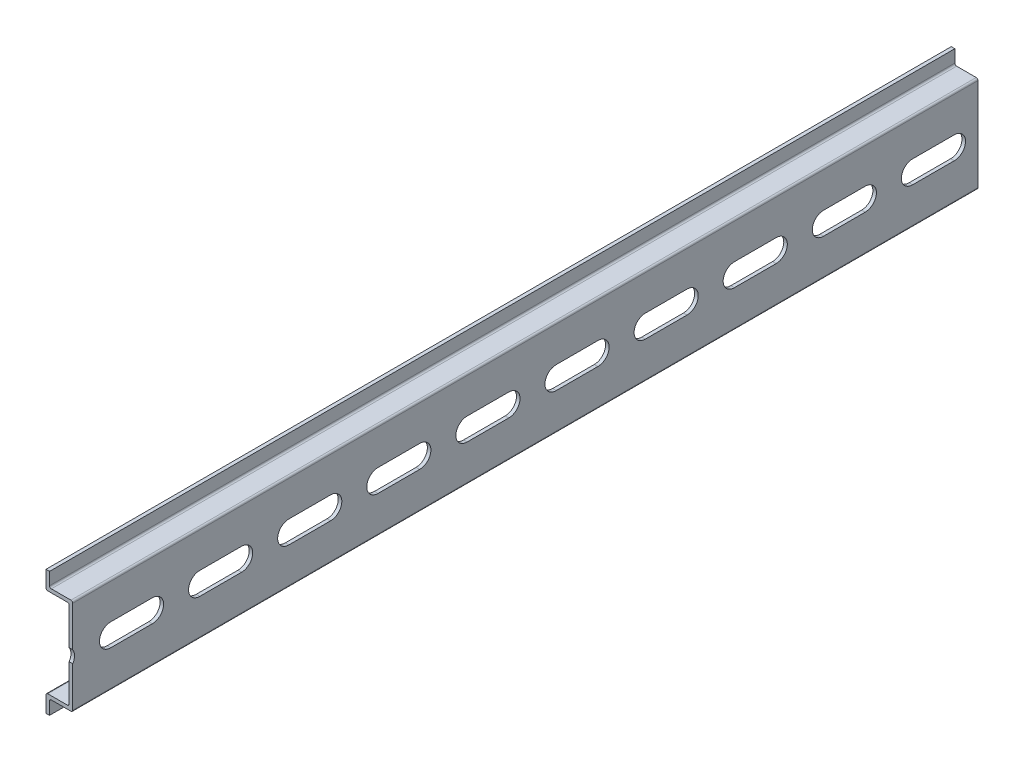
SolidWorks part; units mm, degrees
ref_plane "Front Plane" through (0, 0, 0) normal (0, 0, 1) x (1, 0, 0)
ref_plane "Top Plane" through (0, 0, 0) normal (0, 1, 0) x (1, 0, 0)
ref_plane "Right Plane" through (0, 0, 0) normal (1, 0, 0) x (0, 0, -1)
sketch "profile" plane through (0, 0, 0) normal (0, 0, 1) x (1, 0, 0)
  line L0 (0, -13.5) -> (0, 13.5) construction
  line L1 (0, 13.5) -> (-6.5, 13.5) construction
  line L2 (-6.5, 13.5) -> (-6.5, 17.5) construction
  line L3 (0, -13.5) -> (-6.5, -13.5) construction
  line L4 (-6.5, -13.5) -> (-6.5, -17.5) construction
  dimension "D1" = 27
  dimension "D2" = 35
  dimension "D3" = 6.5
sketch "Sketch3" plane through (0, 0, 0) normal (0, 0, 1) x (1, 0, 0)
  line L0 (-6.5, -13.5) -> (-6.5, -17.5) construction
  line L1 (0, -13.5) -> (-6.5, -13.5) construction
  line L2 (0, -13.5) -> (0, 13.5) construction
  line L3 (0, 13.5) -> (-6.5, 13.5) construction
  line L4 (-6.5, 13.5) -> (-6.5, 17.5) construction
  line L5 (-6.5, -13.5) -> (-6.5, -17.5)
  line L6 (0, -13.5) -> (-6.5, -13.5)
  line L7 (0, -13.5) -> (0, 13.5)
  line L8 (0, 13.5) -> (-6.5, 13.5)
  line L9 (-6.5, 13.5) -> (-6.5, 17.5)
extrude "Extrude-Thin1" add sketch "Sketch3" along normal blind 449.2625 thin
sketch "Sketch4" plane through (0, 0, 0) normal (1, 0, 0) x (0, 0, -1)
  line L0 (0, 0) -> (-62.1077, 0) construction
  line L1 (-6.65, 0) -> (-18.35, 0) construction
  line L2 (-6.65, -3.15) -> (-18.35, -3.15)
  line L3 (-6.65, 3.15) -> (-18.35, 3.15)
  arc A0 (-6.65, -3.15) -> (-6.65, 3.15) centre (-6.65, 0) ccw
  arc A1 (-18.35, 3.15) -> (-18.35, -3.15) centre (-18.35, 0) ccw
  point P5 (-12.5, 0)
  point P10 (-3.5, 0)
  point P11 (-21.5, 0)
  point P12 (-37.5, 0)
  dimension "D1" = 18
  dimension "D2" = 6.3
  dimension "D3" = 12.5
  dimension "D4" = 25
extrude "Cut-Extrude1" cut sketch "Sketch4" against normal through all both and the other way through all
pattern_linear "LPattern1" count 18 spacing 25 along (0, 0, 1) of "Cut-Extrude1"
fillet "Fillet1" radius 0.5 8 edges at (0, -13.5, 224.6312) (0, 13.5, 224.6312) (-6.5, 13.5, 224.6312) (-6.5, -13.5, 224.6312) (-1, 12.5, 224.6312) (-1, -12.5, 224.6312) (-7.5, -12.5, 224.6312) (-7.5, 12.5, 224.6312)
ref_plane "Contact Plane 1" through (-1, 0, 0) normal (-1, 0, 0) x (0, 0, 1)
sketch "Sketch5" plane through (0, 0, 449.2625) normal (0, 0, 1) x (1, 0, 0)
  line L1 (-11.0924, 21.6059) -> (2.0658, 21.6059)
  line L2 (-11.0924, 21.6059) -> (-11.0924, -18.4363)
  line L3 (-11.0924, -18.4363) -> (2.0658, -18.4363)
  line L4 (2.0658, 21.6059) -> (2.0658, -18.4363)
extrude "Cut-Extrude2" cut sketch "Sketch5" against normal blind 195.2625
equation "\"D3@LPattern1\"=\"D4@Sketch4\""
equation "\"D1@LPattern1\" = \"Length@Extrude-Thin1\" / \"D3@LPattern1\""
